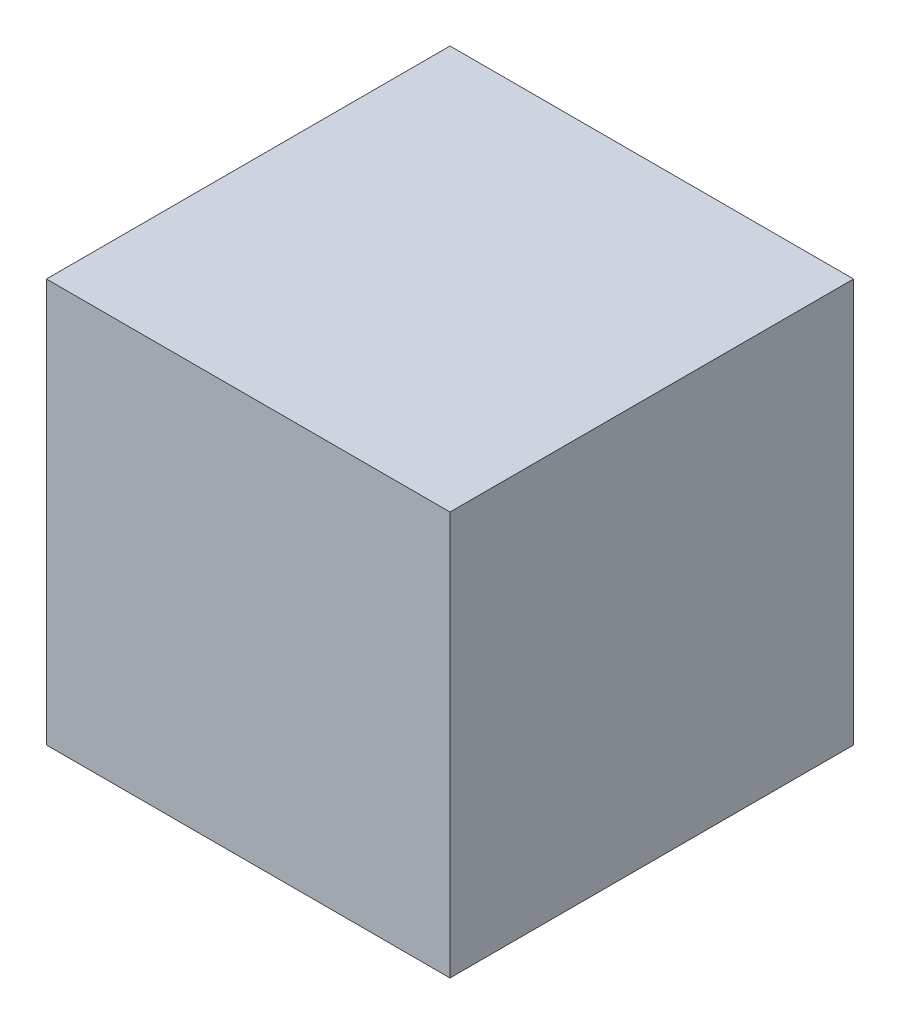
SolidWorks part; units mm, degrees
ref_plane "Plan de face" through (0, 0, 0) normal (0, 0, 1) x (1, 0, 0)
ref_plane "Plan de dessus" through (0, 0, 0) normal (0, 1, 0) x (1, 0, 0)
ref_plane "Plan de droite" through (0, 0, 0) normal (1, 0, 0) x (0, 0, -1)
sketch "Esquisse1" plane through (0, 0, 0) normal (0, 0, 1) x (1, 0, 0)
  line L1 (0, 0) -> (100, 0)
  line L2 (0, 0) -> (0, 100)
  line L3 (0, 100) -> (100, 100)
  line L4 (100, 0) -> (100, 100)
  dimension "D1" = 100
  dimension "D2" = 100
extrude "Boss.-Extru.1" add sketch "Esquisse1" along normal blind 100
